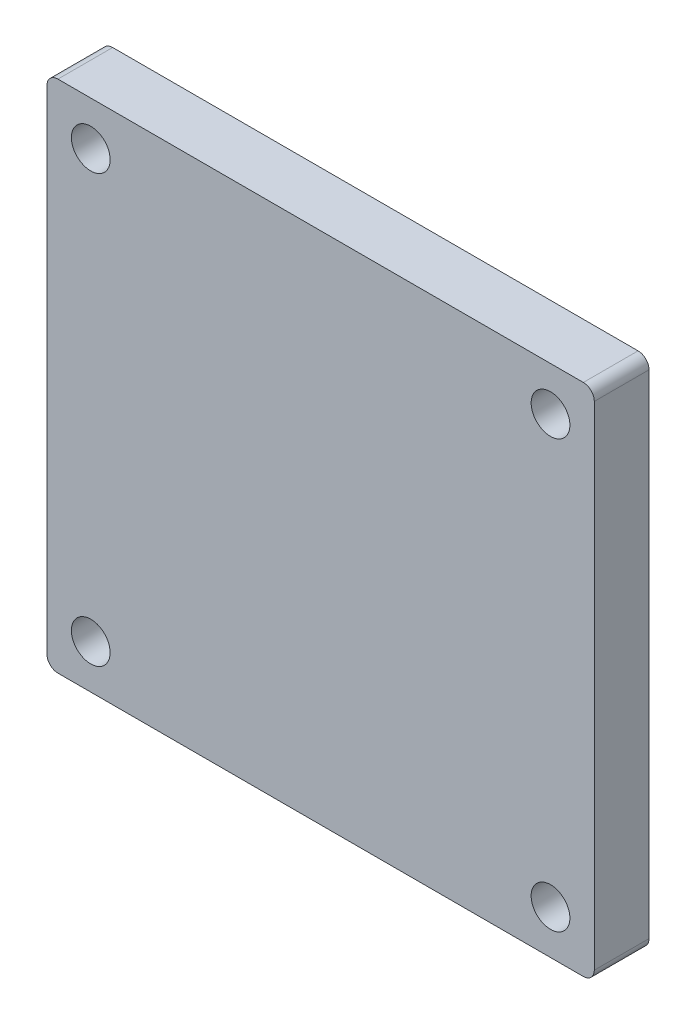
SolidWorks part; units mm, degrees
material "NEOPRENE"
ref_plane "Front Plane" through (0, 0, 0) normal (0, 0, 1) x (1, 0, 0)
ref_plane "Top Plane" through (0, 0, 0) normal (0, 1, 0) x (1, 0, 0)
ref_plane "Right Plane" through (0, 0, 0) normal (1, 0, 0) x (0, 0, -1)
sketch "Sketch1" plane through (0, 0, 0) normal (0, 0, 1) x (1, 0, 0)
  line L0 (6.35, 35.56) -> (6.35, 10.16) construction
  line L1 (0, 0) -> (63.5, 0)
  line L2 (0, 0) -> (0, 59.69)
  line L3 (0, 59.69) -> (63.5, 59.69)
  line L4 (63.5, 0) -> (63.5, 59.69)
  line L5 (6.35, 10.16) -> (57.15, 10.16) construction
  line L6 (57.15, 10.16) -> (57.15, 35.56) construction
  line L7 (57.15, 35.56) -> (6.35, 35.56) construction
  line L8 (31.75, 0) -> (31.75, 10.16) construction
  point P11 (5.08, 54.61)
  point P12 (58.42, 54.61)
  point P13 (58.42, 5.08)
  point P14 (5.08, 5.08)
  dimension "D1" = 5.08
  dimension "D2" = 5.08
  dimension "D3" = 25.4
  dimension "D4" = 50.8
  dimension "D5" = 5.08
  dimension "D6" = 5.08
  dimension "D7" = 5.08
  dimension "D8" = 19.05
  dimension "D9" = 6.35
extrude "Boss-Extrude1" add sketch "Sketch1" along normal blind 6.35
fillet "Fillet1" radius 1.27 4 edges at (0, 0, 3.175) (63.5, 0, 3.175) (63.5, 59.69, 3.175) (0, 59.69, 3.175)
sketch "Sketch6" plane through (0, 0, 6.35) normal (0, 0, 1) x (1, 0, 0)
  line L0 (31.75, 59.69) -> (31.75, 22.225) construction
  line L1 (6.35, 9.525) -> (57.15, 9.525) construction
  line L2 (6.35, 9.525) -> (6.35, 22.225) construction
  line L3 (6.35, 22.225) -> (57.15, 22.225) construction
  line L4 (57.15, 9.525) -> (57.15, 22.225) construction
  line L5 (62.23, 59.69) -> (1.27, 59.69) construction
  line L6 (1.27, 0) -> (62.23, 0) construction
  dimension "D1" = 50.8
  dimension "D2" = 12.7
  dimension "D3" = 9.525
hole_wizard "#8 Clearance Hole1" positions "Sketch5" profile "Sketch4" hole size "#8" standard "ANSI Inch" end condition through all
sketch "Sketch5" plane through (0, 0, 6.35) normal (0, 0, 1) x (1, 0, 0)
  line L5 (31.75, 59.69) -> (31.75, 0) construction
  line L6 (62.23, 59.69) -> (1.27, 59.69) construction
  line L7 (1.27, 0) -> (62.23, 0) construction
  line L10 (0, 29.845) -> (63.5, 29.845) construction
  line L11 (0, 58.42) -> (0, 1.27) construction
  line L12 (63.5, 1.27) -> (63.5, 58.42) construction
  point P78 (5.08, 54.61)
  point P81 (58.42, 54.61)
  point P84 (58.42, 5.08)
  point P87 (5.08, 5.08)
sketch "Sketch4" plane through (5.08, 54.61, 6.35) normal (1, 0, 0) x (0, -1, 0)
  line L0 (0, 0) -> (0, 6.35)
  line L1 (0, 6.35) -> (2.2479, 6.35)
  line L2 (2.2479, 6.35) -> (2.2479, 0)
  line L5 (2.2479, 0) -> (0, 0)
  line L11 (0, -6.35) -> (0, 107.95) construction
  dimension "Thru Hole Dia." = 4.4958
  dimension "Thru Hole Depth" = 6.35
equation "\"pl\"=0.1"
